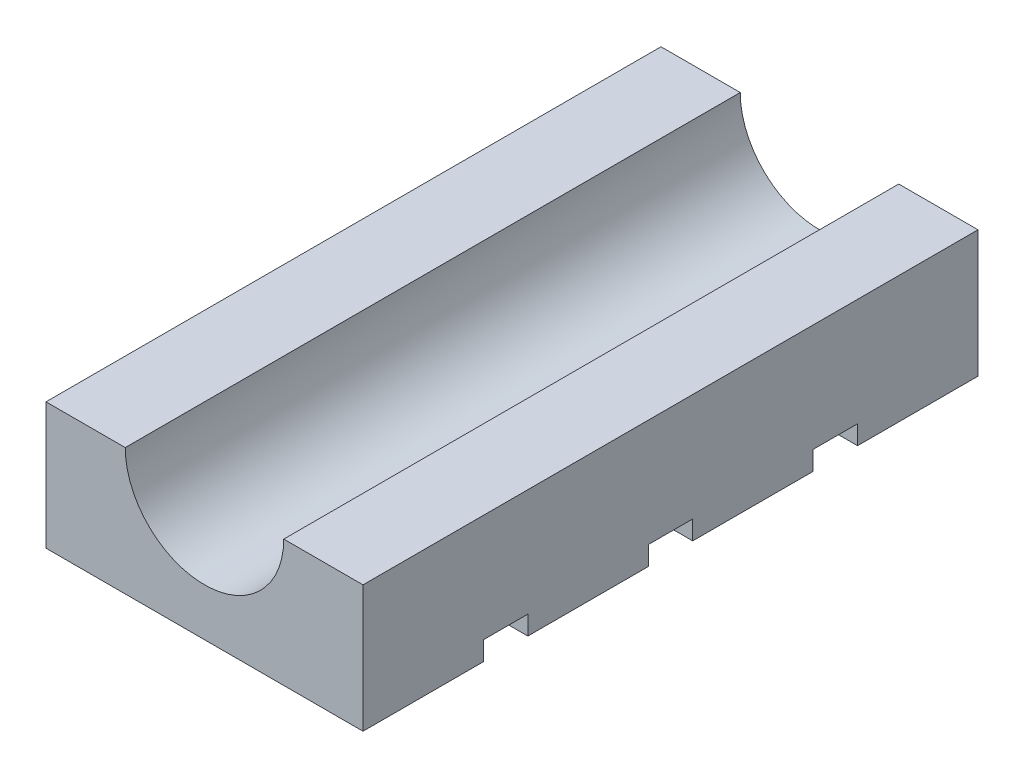
SolidWorks part; units mm, degrees
ref_plane "Front Plane" through (0, 0, 0) normal (0, 0, 1) x (1, 0, 0)
ref_plane "Top Plane" through (0, 0, 0) normal (0, 1, 0) x (1, 0, 0)
ref_plane "Right Plane" through (0, 0, 0) normal (1, 0, 0) x (0, 0, -1)
sketch "Sketch1" plane through (0, 0, 0) normal (0, 1, 0) x (1, 0, 0)
  line L1 (0, 0) -> (50, 0)
  line L2 (0, 0) -> (0, -97)
  line L3 (0, -97) -> (50, -97)
  line L4 (50, 0) -> (50, -97)
  dimension "D1" = 50
  dimension "D2" = 97
extrude "Boss-Extrude1" add sketch "Sketch1" along normal blind 20
sketch "Sketch2" plane through (0, 0, 97) normal (0, 0, 1) x (1, 0, 0)
  line L0 (0, 20) -> (50, 20) construction
  circle A0 centre (25, 20) radius 12.5
  dimension "D1" = 25
extrude "Cut-Extrude1" cut sketch "Sketch2" against normal blind 100
sketch "Sketch3" plane through (0, 0, 0) normal (0, -1, 0) x (1, 0, 0)
  line L0 (0, 0) -> (0, 97) construction
  line L1 (0, 78) -> (50, 78)
  line L2 (0, 78) -> (0, 71)
  line L3 (0, 71) -> (50, 71)
  line L4 (50, 78) -> (50, 71)
  line L5 (50, 97) -> (50, 0) construction
  line L6 (50, 0) -> (0, 0) construction
  line L7 (0, 52) -> (50, 52)
  line L8 (0, 52) -> (0, 45)
  line L9 (0, 45) -> (50, 45)
  line L10 (50, 52) -> (50, 45)
  line L11 (0, 26) -> (50, 26)
  line L12 (0, 26) -> (0, 19)
  line L13 (0, 19) -> (50, 19)
  line L14 (50, 26) -> (50, 19)
  line L16 (0, 97) -> (50, 97) construction
  dimension "D1" = 7
  dimension "D2" = 7
  dimension "D3" = 7
  dimension "D4" = 45
  dimension "D5" = 19
  dimension "D6" = 19
extrude "Cut-Extrude2" cut sketch "Sketch3" against normal blind 3
